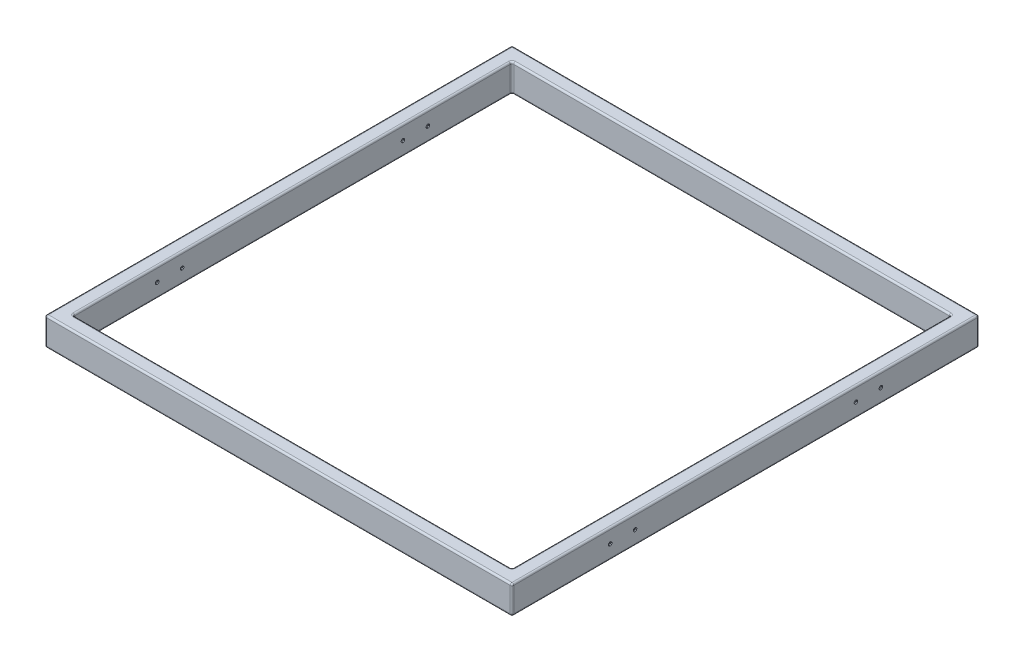
SolidWorks part; units mm, degrees
material "Plain Carbon Steel"
ref_plane "Front" through (0, 0, 0) normal (0, 0, 1) x (1, 0, 0)
ref_plane "Top" through (0, 0, 0) normal (0, 1, 0) x (1, 0, 0)
ref_plane "Right" through (0, 0, 0) normal (1, 0, 0) x (0, 0, -1)
sketch "Sketch1" plane through (0, 0, 0) normal (0, 1, 0) x (1, 0, 0)
  line L1 (-665, 665) -> (665, 665)
  line L2 (-665, 665) -> (-665, -665)
  line L3 (-665, -665) -> (665, -665)
  line L4 (665, 665) -> (665, -665)
  line L5 (-665, 665) -> (665, -665) construction
  line L6 (-665, -665) -> (665, 665) construction
  line L7 (-625, 625) -> (625, 625)
  line L8 (-625, 625) -> (-625, -625)
  line L9 (-625, -625) -> (625, -625)
  line L10 (625, 625) -> (625, -625)
  line L11 (-625, 625) -> (625, -625) construction
  line L12 (-625, -625) -> (625, 625) construction
  point P0 (0, 0)
  point P6 (0, 0)
  dimension "D1" = 1330
  dimension "D2" = 40
extrude "Boss-Extrude1" add sketch "Sketch1" along normal blind 80
fillet "Fillet1" radius 5 24 edges at (-665, 40, 665) (665, 40, 665) (0, 0, 665) (0, 80, 665) (-665, 80, 0) (0, 80, -665) (665, 80, 0) (-625, 80, 0) (0, 80, 625) (625, 80, 0) (0, 80, -625) (665, 40, -665) (-665, 40, -665) (-665, 0, 0) (0, 0, -665) (665, 0, 0) (625, 40, -625) (-625, 40, -625) (-625, 40, 625) (625, 40, 625) (0, 0, 625) (-625, 0, 0) (0, 0, -625) (625, 0, 0)
shell "Shell1" thickness 3
sketch "Sketch2" plane through (665, 0, 0) normal (1, 0, 0) x (0, 0, -1)
  circle A0 centre (-350, 60) radius 9
  circle A1 centre (0, 60) radius 9
  circle A2 centre (350, 60) radius 9
  dimension "D1" = 18
sketch "Sketch3" plane through (-665, 0, 0) normal (-1, 0, 0) x (0, 0, 1)
  circle A1 centre (-350, 60) radius 9
  circle A2 centre (-350, 60) radius 9
  circle A3 centre (0, 60) radius 9
  circle A4 centre (0, 60) radius 9
  circle A5 centre (350, 60) radius 9
  circle A6 centre (350, 60) radius 9
  dimension "D1" = 0
  dimension "D2" = 0
  dimension "D3" = 0
sketch "Sketch4" plane through (-665, 0, 0) normal (-1, 0, 0) x (0, 0, 1)
  line L0 (0, 0) -> (0, 75) construction
  line L1 (660, 75) -> (-660, 75) construction
  circle A0 centre (385.5, 40) radius 5
  circle A1 centre (314.5, 40) radius 5
  circle A2 centre (-314.5, 40) radius 5
  circle A3 centre (-385.5, 40) radius 5
  dimension "D1" = 10
extrude "Cut-Extrude1" cut sketch "Sketch4" against normal up to surface (40 mm away) up to face at (-625, 40, 0)
sketch "Sketch5" plane through (665, 0, 0) normal (1, 0, 0) x (0, 0, -1)
  circle A1 centre (385.5, 40) radius 5
  circle A2 centre (385.5, 40) radius 5
  circle A3 centre (314.5, 40) radius 5
  circle A4 centre (314.5, 40) radius 5
  circle A5 centre (-314.5, 40) radius 5
  circle A6 centre (-314.5, 40) radius 5
  circle A7 centre (-385.5, 40) radius 5
  circle A8 centre (-385.5, 40) radius 5
  dimension "D1" = 0
  dimension "D2" = 0
  dimension "D3" = 0
  dimension "D4" = 0
extrude "Cut-Extrude2" cut sketch "Sketch5" against normal up to surface (40 mm away) up to face at (625, 40, 0)
